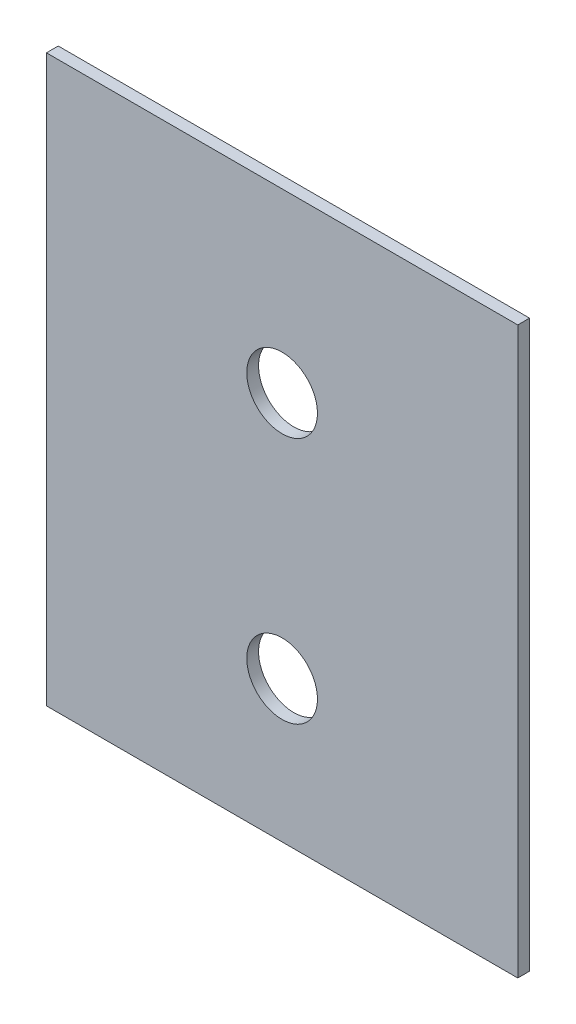
SolidWorks part; units mm, degrees
ref_plane "Front Plane" through (0, 0, 0) normal (0, 0, 1) x (1, 0, 0)
ref_plane "Top Plane" through (0, 0, 0) normal (0, 1, 0) x (1, 0, 0)
ref_plane "Right Plane" through (0, 0, 0) normal (1, 0, 0) x (0, 0, -1)
sketch "Sketch1" plane through (0, 0, 0) normal (0, 0, 1) x (1, 0, 0)
  line L0 (0, 240) -> (400, 240) construction
  line L5 (0, 0) -> (400, 0)
  line L6 (0, 0) -> (0, 480)
  line L7 (0, 480) -> (400, 480)
  line L8 (400, 0) -> (400, 480)
  circle A0 centre (200, 330) radius 30
  circle A1 centre (200, 120) radius 30
  dimension "D4" = 60
  dimension "D5" = 60
  dimension "D7" = 200
  dimension "D8" = 150
  dimension "D9" = 200
  dimension "D1" = 400
  dimension "D2" = 480
  dimension "D3" = 240
  dimension "D6" = 120
extrude "Extrude1" add sketch "Sketch1" along normal blind 10
